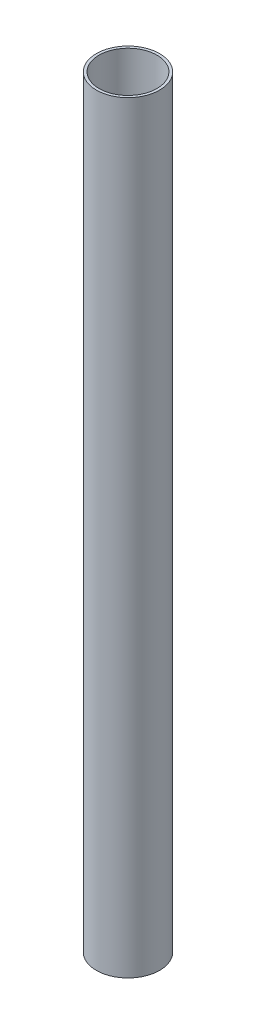
SolidWorks part; units mm, degrees
ref_plane "Front Plane" through (0, 0, 0) normal (0, 0, 1) x (1, 0, 0)
ref_plane "Top Plane" through (0, 0, 0) normal (0, 1, 0) x (1, 0, 0)
ref_plane "Right Plane" through (0, 0, 0) normal (1, 0, 0) x (0, 0, -1)
sketch "Sketch1" plane through (0, 0, 0) normal (0, 1, 0) x (1, 0, 0)
  circle A0 centre (0, 0) radius 38
  circle A1 centre (0, 0) radius 41.5
  dimension "D1" = 76
  dimension "D2" = 83
  dimension "D3" = 3.5
extrude "Boss-Extrude1" add sketch "Sketch1" along normal blind 1000
